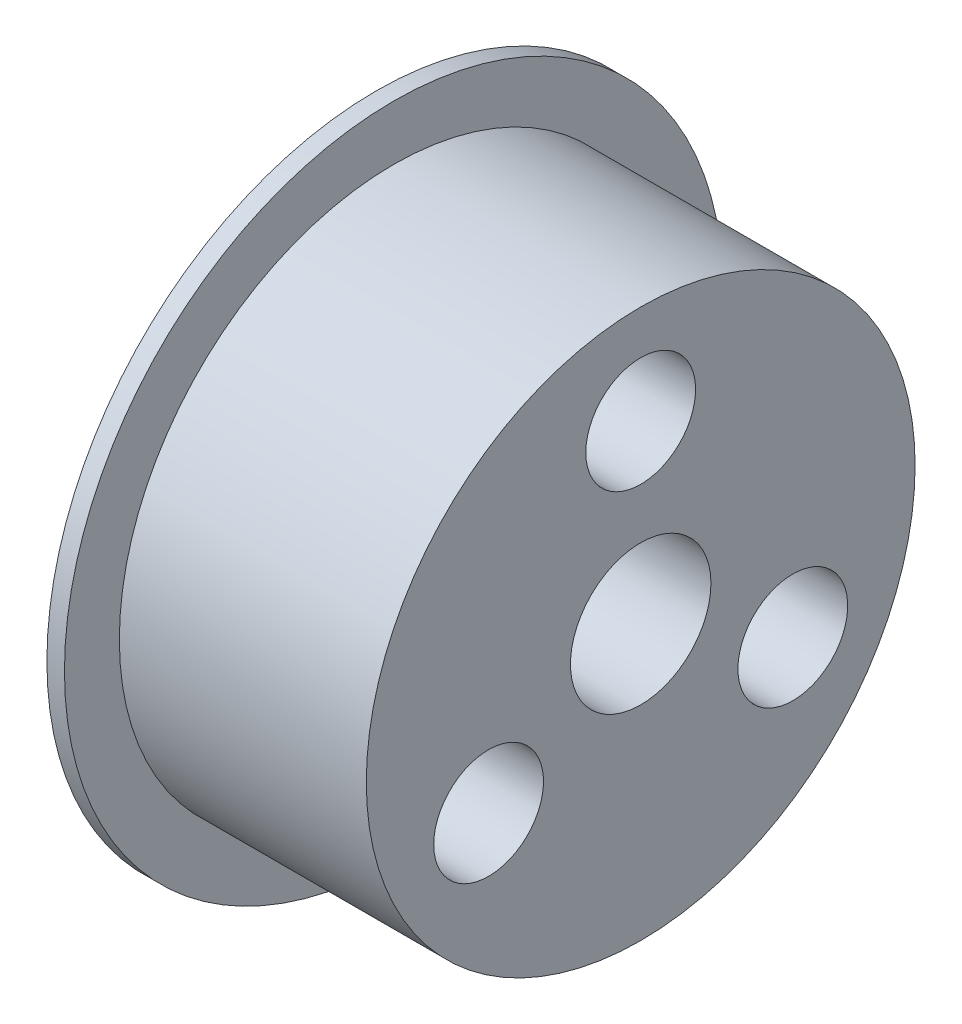
SolidWorks part; units mm, degrees
material "PET"
ref_plane "Front" through (0, 0, 0) normal (0, 0, 1) x (1, 0, 0)
ref_plane "Top" through (0, 0, 0) normal (0, 1, 0) x (1, 0, 0)
ref_plane "Right" through (0, 0, 0) normal (1, 0, 0) x (0, 0, -1)
sketch "Sketch1" plane through (0, 0, 0) normal (0, 0, 1) x (1, 0, 0)
  line L0 (0, 4.064) -> (-15.3035, 4.064)
  line L1 (-15.3035, 4.064) -> (-15.3035, 19.05)
  line L2 (-15.3035, 19.05) -> (-14.2875, 19.05)
  line L3 (-14.2875, 19.05) -> (-14.2875, 15.875)
  line L4 (-14.2875, 15.875) -> (0, 15.875)
  line L5 (0, 15.875) -> (0, 4.064)
  line L6 (0, 0) -> (-17.901, 0) construction
  dimension "D1" = 8.128
  dimension "D2" = 31.75
  dimension "D3" = 3.175
  dimension "D4" = 1.016
  dimension "D5" = 14.2875
revolve "Revolve1" add sketch "Sketch1" angle 360 about L6
sketch "Sketch4" plane through (-15.3035, 0, 0) normal (-1, 0, 0) x (0, 0, 1)
  circle A0 centre (0, 0) radius 10.16 construction
  point P0 (0, 10.16)
  point P10 (8.7988, -5.08)
  point P11 (-8.7988, -5.08)
  dimension "D1" = 20.32
  dimension "D2" = 3
hole_wizard "CBORE for #10 Socket Head Cap Screw1" positions "Sketch4" profile "Sketch3" counterbore size "#10" standard "ANSI Inch"
sketch "Sketch3" plane through (-15.3035, 10.16, 0) normal (0, 1, 0) x (0, 0, 1)
  line L0 (0, 0) -> (0, 15.3035)
  line L1 (0, 15.3035) -> (2.5527, 15.3035)
  line L3 (2.5527, 15.3035) -> (2.5527, 6.35)
  line L4 (2.5527, 6.35) -> (4.7625, 6.35)
  line L5 (4.7625, 6.35) -> (4.7625, 0)
  line L7 (4.7625, 0) -> (0, 0)
  line L11 (0, -6.35) -> (0, 107.95) construction
  dimension "Thru Hole Dia." = 5.1054
  dimension "Thru Hole Depth" = 15.3035
  dimension "C'Bore Dia." = 9.525
  dimension "C'Bore Depth" = 6.35
sketch "Sketch7" plane through (-15.3035, 0, 0) normal (-1, 0, 0) x (0, 0, 1)
  point P0 (0, 10.16)
  point P5 (8.7988, -5.08)
  point P8 (-8.7988, -5.08)
hole_wizard "1/4 (0.2500) Dowel Hole1" positions "Sketch7" profile "Sketch6" hole size "1/4" standard "ANSI Inch" end condition through all
sketch "Sketch6" plane through (-15.3035, 10.16, 0) normal (0, 1, 0) x (0, 0, 1)
  line L0 (0, 0) -> (0, 15.3035)
  line L1 (0, 15.3035) -> (3.175, 15.3035)
  line L2 (3.175, 15.3035) -> (3.175, 0)
  line L5 (3.175, 0) -> (0, 0)
  line L11 (0, -6.35) -> (0, 107.95) construction
  dimension "Thru Hole Dia." = 6.35
  dimension "Thru Hole Depth" = 15.3035
